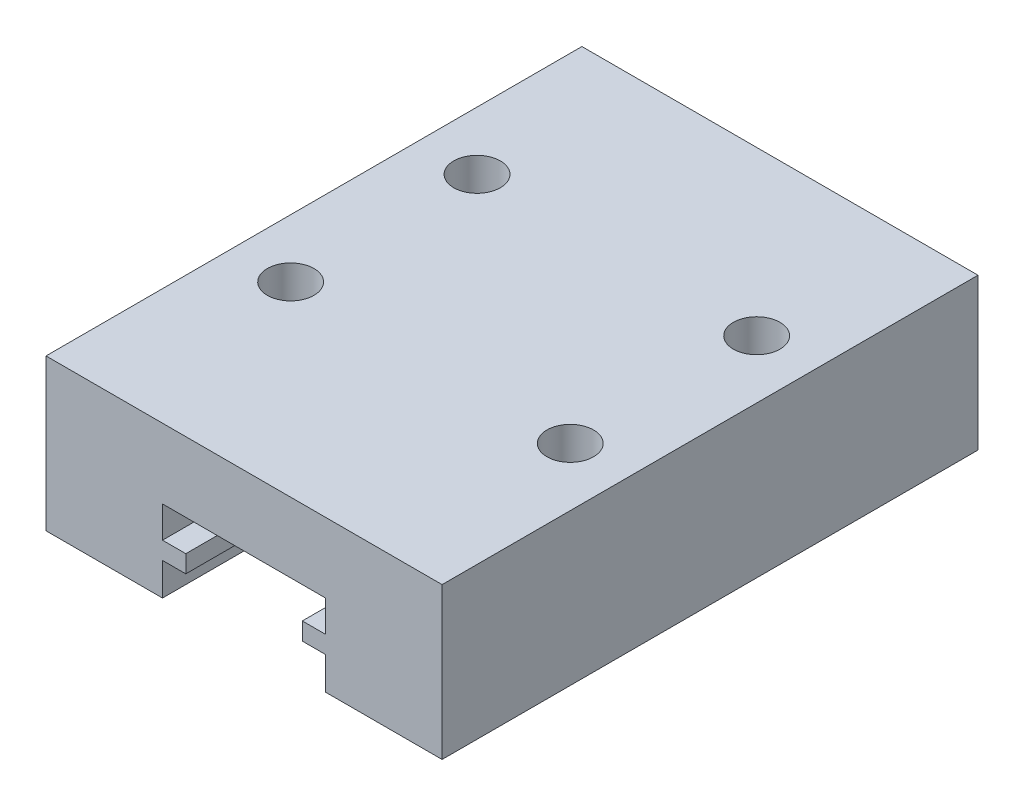
SolidWorks part; units mm, degrees
material "普通碳钢"
ref_plane "前视基准面" through (0, 0, 0) normal (0, 0, 1) x (1, 0, 0)
ref_plane "上视基准面" through (0, 0, 0) normal (0, 1, 0) x (1, 0, 0)
ref_plane "右视基准面" through (0, 0, 0) normal (1, 0, 0) x (0, 0, -1)
sketch "草图1" plane through (0, 0, 0) normal (0, 0, 1) x (1, 0, 0)
  line L0 (3.5, -3.25) -> (3.5, -1.85)
  line L1 (-8.5, 3.25) -> (8.5, 3.25)
  line L2 (-8.5, 3.25) -> (-8.5, -3.25)
  line L3 (-8.5, -3.25) -> (8.5, -3.25)
  line L4 (8.5, 3.25) -> (8.5, -3.25)
  line L5 (3.5, -1.85) -> (2.5, -1.85)
  line L6 (2.5, -1.85) -> (2.5, -1.1)
  line L7 (2.5, -1.1) -> (3.5, -1.1)
  line L8 (3.5, -1.1) -> (3.5, 0.25)
  line L9 (3.5, 0.25) -> (-3.5, 0.25)
  line L10 (0, -55) -> (0, 55) construction
  line L11 (-3.5, -1.1) -> (-3.5, 0.25)
  line L12 (-2.5, -1.1) -> (-3.5, -1.1)
  line L13 (-2.5, -1.85) -> (-2.5, -1.1)
  line L14 (-3.5, -1.85) -> (-2.5, -1.85)
  line L15 (-3.5, -3.25) -> (-3.5, -1.85)
  point P16 (0, 0.25)
  dimension "D1" = 6.5
  dimension "D2" = 3.25
  dimension "D3" = 17
  dimension "D4" = 8.5
  dimension "D5" = 1
  dimension "D6" = 3.5
  dimension "D7" = 0.75
  dimension "D8" = 1.35
  dimension "D9" = 3
extrude "凸台-拉伸1" add sketch "草图1" along normal blind 23 contours L3 L15 L14 L13 L12 L11 L9 L8 L7 L6 L5 L0 L4 L1 L2
sketch "草图2" plane through (0, 0, 0) normal (0, 1, 0) x (1, 0, 0)
  line L0 (0, -3.575) -> (0, 3.575) construction
  circle A0 centre (-6, -7) radius 1
  circle A1 centre (6, -7) radius 1
  circle A2 centre (-6, -15) radius 1
  circle A3 centre (6, -15) radius 1
  dimension "D1" = 2
  dimension "D2" = 6
  dimension "D3" = 7
  dimension "D4" = 2
extrude "切除-拉伸1" cut sketch "草图2" against normal blind 3 from surface at 3.25 starting at face at (0, 3.25, 11.5)
